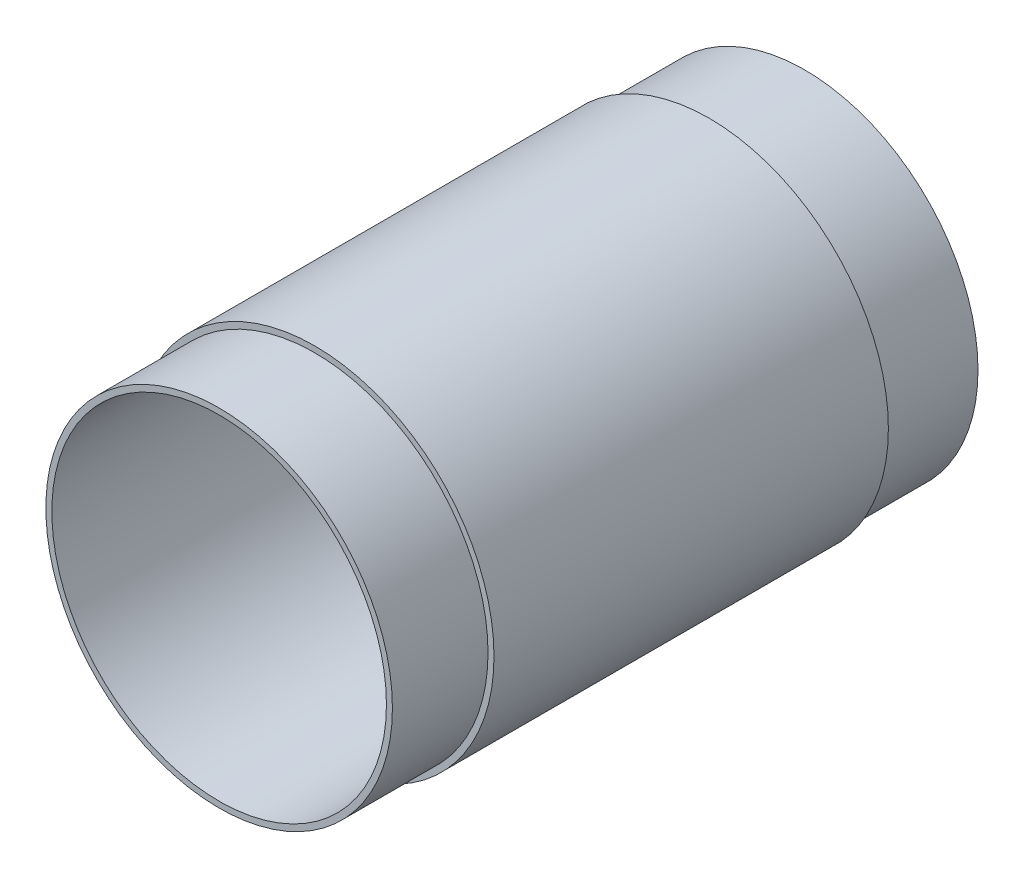
SolidWorks part; units mm, degrees
material "1060 Alloy"
ref_plane "Front Plane" through (0, 0, 0) normal (0, 0, 1) x (1, 0, 0)
ref_plane "Top Plane" through (0, 0, 0) normal (0, 1, 0) x (1, 0, 0)
ref_plane "Right Plane" through (0, 0, 0) normal (1, 0, 0) x (0, 0, -1)
sketch "Sketch1" plane through (0, 0, 0) normal (1, 0, 0) x (0, 0, -1)
  line L0 (0, 14) -> (49, 14)
  line L1 (49, 14) -> (49, 14.5)
  line L2 (49, 14.5) -> (41, 14.5)
  line L3 (41, 14.5) -> (41, 15)
  line L4 (41, 15) -> (8, 15)
  line L5 (8, 15) -> (8, 14.5)
  line L6 (8, 14.5) -> (0, 14.5)
  line L7 (0, 14.5) -> (0, 14)
  line L8 (0, 0) -> (54, 0) construction
  dimension "D1" = 49
  dimension "D2" = 14
  dimension "D3" = 1
  dimension "D4" = 0.5
  dimension "D5" = 8
revolve "Revolve1" add sketch "Sketch1" angle 360 about L8
